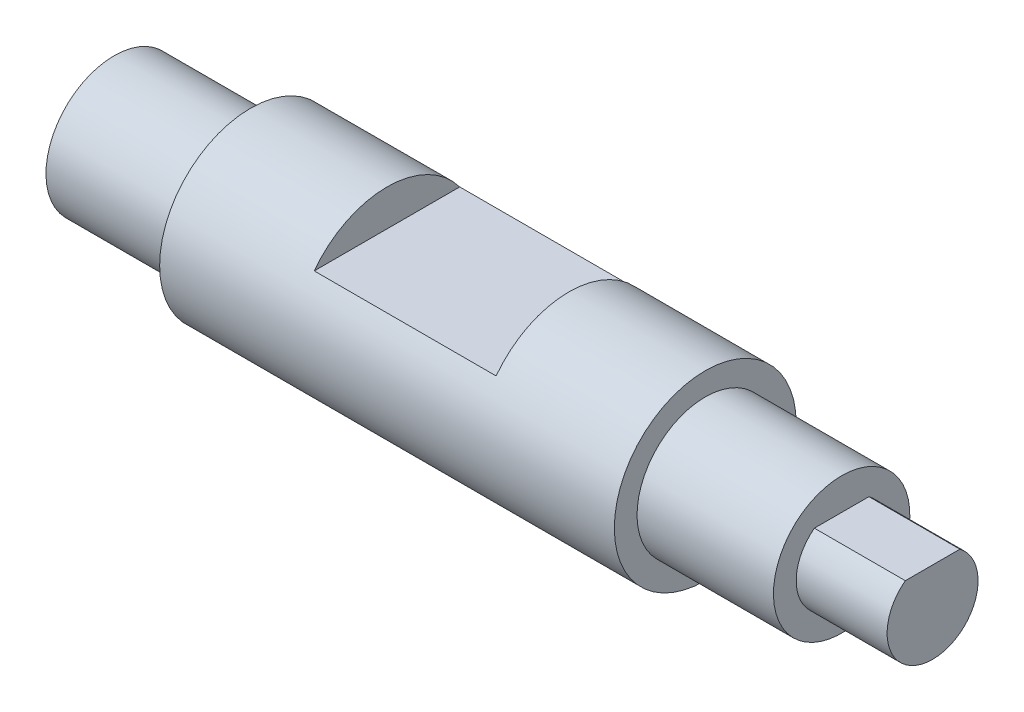
SolidWorks part; units mm, degrees
ref_plane "Ön Düzlem" through (0, 0, 0) normal (0, 0, 1) x (1, 0, 0)
ref_plane "Üst Düzlem" through (0, 0, 0) normal (0, 1, 0) x (1, 0, 0)
ref_plane "Sağ Düzlem" through (0, 0, 0) normal (1, 0, 0) x (0, 0, -1)
sketch "Çizim1" plane through (0, 0, 0) normal (0, 0, 1) x (1, 0, 0)
  line L0 (0, 0) -> (0, 7.5)
  line L1 (0, 7.5) -> (15, 7.5)
  line L2 (15, 7.5) -> (15, 10)
  line L3 (15, 10) -> (65, 10)
  line L4 (65, 10) -> (65, 7.5)
  line L5 (65, 7.5) -> (80, 7.5)
  line L6 (80, 7.5) -> (80, 5)
  line L7 (80, 5) -> (90, 5)
  line L8 (90, 5) -> (90, 0)
  line L9 (90, 0) -> (0, 0)
  dimension "D1" = 50
  dimension "D2" = 15
  dimension "D3" = 15
  dimension "D4" = 10
  dimension "D5" = 5
  dimension "D6" = 7.5
  dimension "D7" = 7.5
  dimension "D8" = 10
revolve "Döndür2" add sketch "Çizim1" angle 360 about L9
sketch "Çizim3" plane through (0, 0, 0) normal (0, 0, 1) x (1, 0, 0)
  line L0 (80, -7.5) -> (80, 7.5) construction
  line L1 (30, 14.9565) -> (50, 14.9565)
  line L2 (30, 14.9565) -> (30, 6)
  line L3 (30, 6) -> (50, 6)
  line L4 (50, 14.9565) -> (50, 6)
  line L5 (80, 4) -> (96.2331, 4)
  line L6 (80, 4) -> (80, 11.0256)
  line L7 (80, 11.0256) -> (96.2331, 11.0256)
  line L8 (96.2331, 4) -> (96.2331, 11.0256)
  dimension "D1" = 20
  dimension "D2" = 15
  dimension "D3" = 6
  dimension "D4" = 4
extrude "Kes-Ekstrüzyon1" cut sketch "Çizim3" against normal mid plane 60
